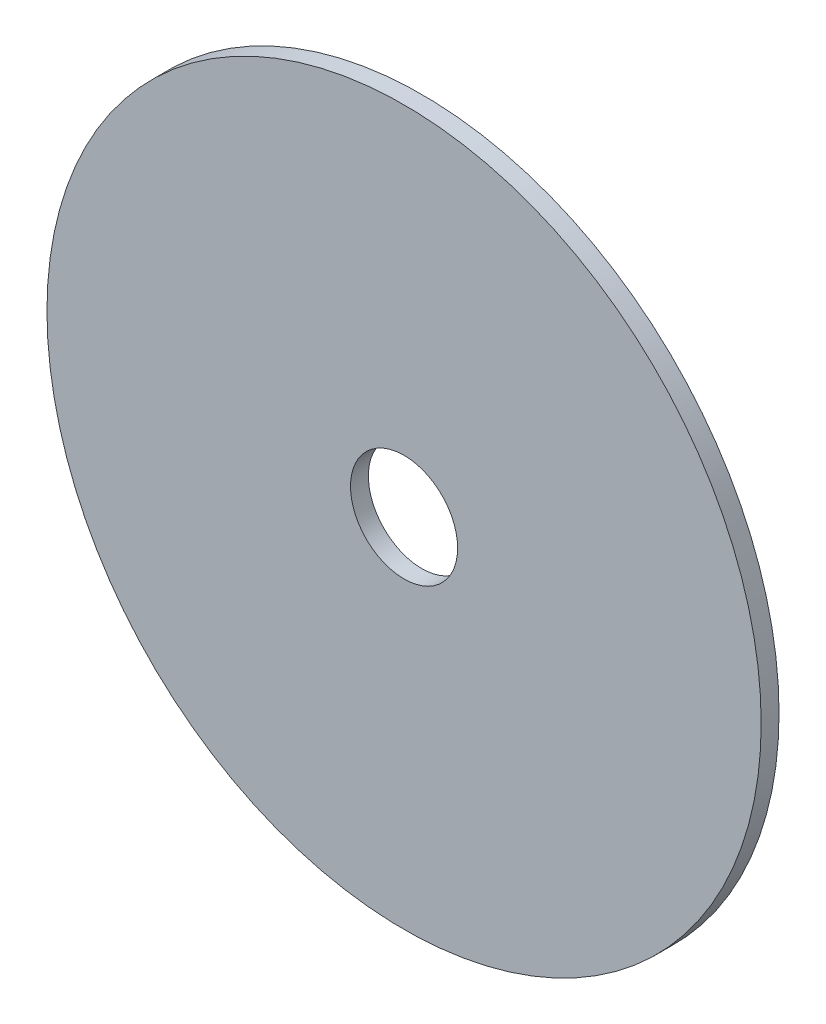
SolidWorks part; units mm, degrees
ref_plane "Front Plane" through (0, 0, 0) normal (0, 0, 1) x (1, 0, 0)
ref_plane "Top Plane" through (0, 0, 0) normal (0, 1, 0) x (1, 0, 0)
ref_plane "Right Plane" through (0, 0, 0) normal (1, 0, 0) x (0, 0, -1)
sketch "Sketch2" plane through (0, 0, 0) normal (0, 0, 1) x (1, 0, 0)
  circle A0 centre (0, 0) radius 15
  circle A1 centre (0, 0) radius 100
extrude "Boss-Extrude1" add sketch "Sketch2" along normal blind 5
